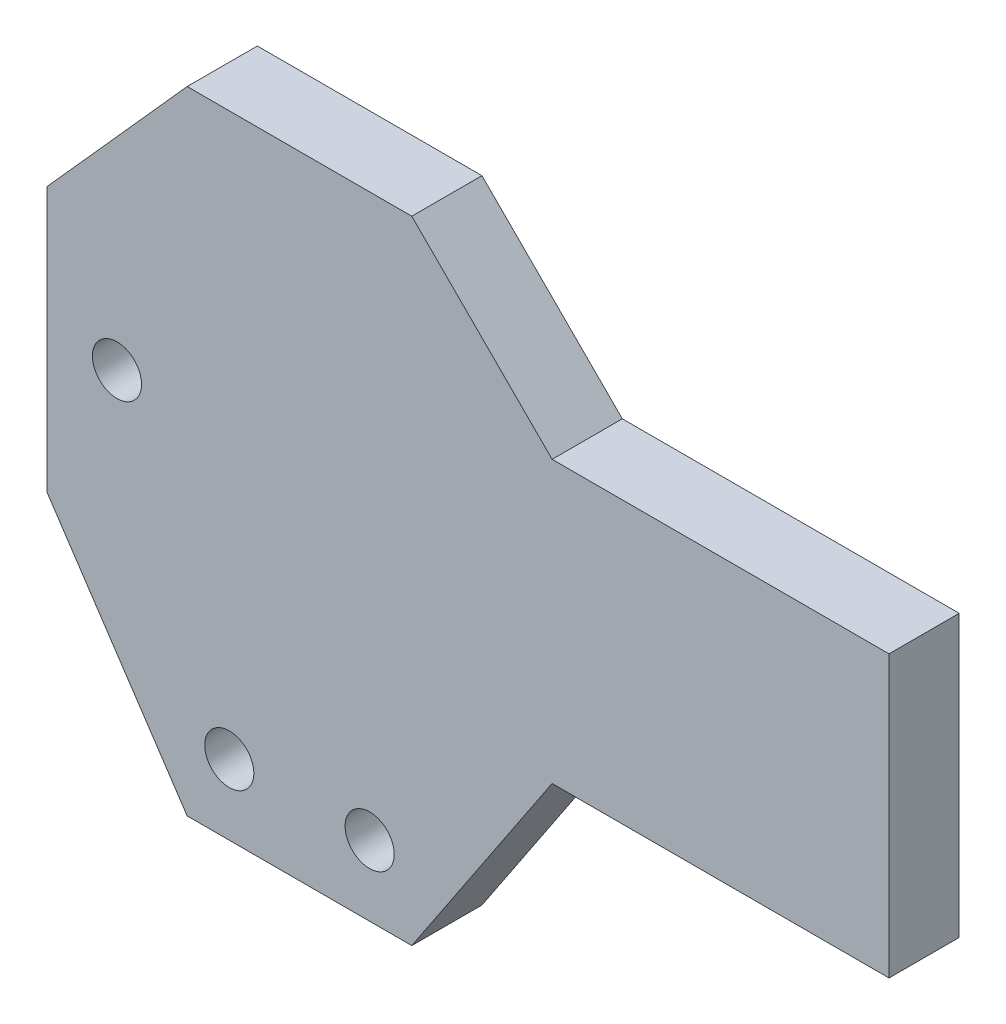
SolidWorks part; units mm, degrees
material "Cast Alloy Steel"
ref_plane "Front Plane" through (0, 0, 0) normal (0, 0, 1) x (1, 0, 0)
ref_plane "Top Plane" through (0, 0, 0) normal (0, 1, 0) x (1, 0, 0)
ref_plane "Right Plane" through (0, 0, 0) normal (1, 0, 0) x (0, 0, -1)
sketch "Sketch1" plane through (0, 0, 0) normal (0, 0, 1) x (1, 0, 0)
  line L0 (-30, 11.3197) -> (-20, 22.5)
  line L1 (-30, 22.5) -> (30, 22.5)
  line L2 (-30, 22.5) -> (-30, -22.5)
  line L3 (-30, -22.5) -> (30, -22.5)
  line L4 (30, 22.5) -> (30, -22.5)
  line L5 (-30, 22.5) -> (30, -22.5) construction
  line L6 (-30, -22.5) -> (30, 22.5) construction
  line L7 (-30, -7.5) -> (-20, -22.5)
  line L8 (-4, -22.5) -> (6, -7.5)
  line L9 (6, -7.5) -> (30, -7.5)
  line L10 (-4, 22.5) -> (6, 12.5)
  line L11 (6, 12.5) -> (30, 12.5)
  line L12 (-26.75, 2.5) -> (30, 2.5) construction
  line L13 (7.3, 7.9) -> (7.3, -2.9)
  line L14 (-3.5, 7.9) -> (14.5, 7.9)
  line L15 (-3.5, 7.9) -> (-3.5, -2.9)
  line L16 (-3.5, -2.9) -> (14.5, -2.9)
  line L17 (14.5, 7.9) -> (14.5, -2.9)
  line L18 (-3.5, 7.9) -> (14.5, -2.9) construction
  line L19 (-3.5, -2.9) -> (14.5, 7.9) construction
  circle A0 centre (-17, -17.5) radius 1.75
  circle A1 centre (-7, -17.5) radius 1.75
  circle A2 centre (-25, 2.5) radius 1.75
  point P0 (0, 0)
  point P24 (5.5, 2.5)
  dimension "D13" = 3.5
  dimension "D1" = 60
  dimension "D2" = 45
  dimension "D3" = 15
  dimension "D4" = 10
  dimension "D5" = 10
  dimension "D6" = 16
  dimension "D7" = 10
  dimension "D8" = 20
  dimension "D9" = 10
  dimension "D10" = 16
  dimension "D11" = 15
  dimension "D12" = 10
  dimension "D14" = 10
  dimension "D15" = 5
  dimension "D16" = 5
  dimension "D17" = 15.5
  dimension "D18" = 18
  dimension "D19" = 4.6
  dimension "D20" = 10
  dimension "D21" = 3
  dimension "D22" = 10.8
extrude "Boss-Extrude3" add sketch "Sketch1" along normal blind 5 contours L17 L14 L13 L16 | L11 L10 L1 L0 L2 L7 L3 L8 L9 L4 A2 A1 A0 L14 L17 L16 L15
sketch "Sketch2" plane through (0, 0, 0) normal (0, 0, -1) x (-1, 0, 0)
  line L0 (-6, -7.5) -> (-30, -7.5) construction
  line L1 (-30, 12.5) -> (20, 12.5)
  line L2 (-30, 12.5) -> (-30, -7.5)
  line L3 (-30, -7.5) -> (20, -7.5)
  line L4 (20, 12.5) -> (20, -7.5)
extrude "Boss-Extrude4" add sketch "Sketch2" against normal up to surface (5 mm away) up to face at (1.9, 2.5, 5)
sketch "Sketch3" plane through (0, 0, 0) normal (0, 0, -1) x (-1, 0, 0)
  line L0 (30, 11.3197) -> (30, -7.5) construction
  line L1 (7.7538, -10.8603) -> (-39.2462, -10.8603)
  line L2 (7.7538, -10.8603) -> (7.7538, 16.1397)
  line L3 (7.7538, 16.1397) -> (-39.2462, 16.1397)
  line L4 (-39.2462, -10.8603) -> (-39.2462, 16.1397)
  circle A0 centre (-1.9, 2.5) radius 1.75
  circle A1 centre (25, 2.5) radius 1.75 construction
  circle A2 centre (25, 2.5) radius 1.75
  dimension "D2" = 3.5
  dimension "D1" = 26.9
  dimension "D3" = 27
  dimension "D4" = 47
  dimension "D5" = 22.2462
